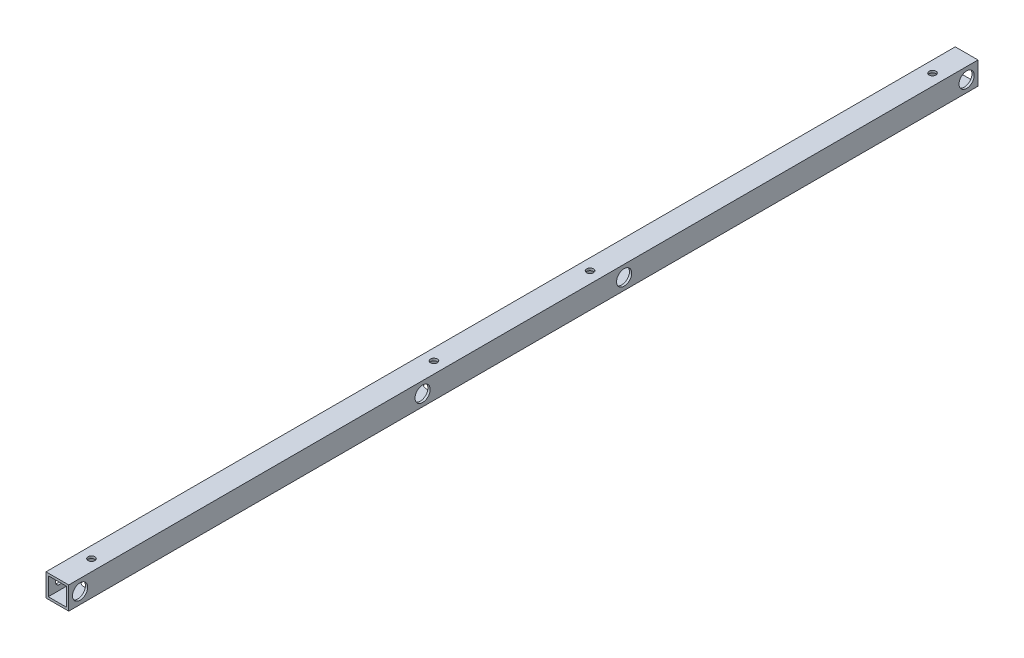
SolidWorks part; units mm, degrees
material "6063-T5"
ref_plane "正面" through (0, 0, 0) normal (0, 0, 1) x (1, 0, 0)
ref_plane "平面" through (0, 0, 0) normal (0, 1, 0) x (1, 0, 0)
ref_plane "右側面" through (0, 0, 0) normal (1, 0, 0) x (0, 0, -1)
sketch "ｽｹｯﾁ1" plane through (0, 0, 0) normal (0, 0, 1) x (1, 0, 0)
  line L1 (-7.5, -7.5) -> (7.5, -7.5)
  line L2 (-7.5, -7.5) -> (-7.5, 7.5)
  line L3 (-7.5, 7.5) -> (7.5, 7.5)
  line L4 (7.5, -7.5) -> (7.5, 7.5)
  line L5 (-7.5, -7.5) -> (7.5, 7.5) construction
  line L6 (-7.5, 7.5) -> (7.5, -7.5) construction
  line L7 (-6, -6) -> (6, -6)
  line L8 (-6, -6) -> (-6, 6)
  line L9 (-6, 6) -> (6, 6)
  line L10 (6, -6) -> (6, 6)
  line L11 (-6, -6) -> (6, 6) construction
  line L12 (-6, 6) -> (6, -6) construction
  point P0 (0, 0)
  point P6 (0, 0)
  dimension "D1" = 1.5
  dimension "D2" = 15
  dimension "D3" = 15
extrude "ﾎﾞｽ - 押し出し1" add sketch "ｽｹｯﾁ1" along normal blind 600
sketch "ｽｹｯﾁ2" plane through (7.5, 0, 0) normal (1, 0, 0) x (0, 0, -1)
  line L0 (-600, -7.5) -> (0, -7.5) construction
  line L1 (0, -7.5) -> (0, 7.5) construction
  line L2 (-600, -7.5) -> (-600, 7.5) construction
  circle A4 centre (-592.5, 0) radius 2.7
  circle A8 centre (-7.5, 0) radius 2.7
  dimension "D1" = 5.4
  dimension "D2" = 7.5
  dimension "D3" = 7.5
  dimension "D4" = 7.5
  dimension "D9" = 2
extrude "ｶｯﾄ - 押し出し1" cut sketch "ｽｹｯﾁ2" against normal blind 25
sketch "ｽｹｯﾁ3" plane through (0, 7.5, 0) normal (0, 1, 0) x (1, 0, 0)
  line L1 (-7.5, -600) -> (-7.5, 0) construction
  line L2 (7.5, -600) -> (7.5, 0) construction
  line L3 (7.5, 0) -> (-7.5, 0) construction
  circle A1 centre (0, -22.5) radius 2.25
  circle A6 centre (0, -577.5) radius 2.25
  circle A7 centre (0, -248.5) radius 2.25
  circle A8 centre (0, -351.5) radius 2.25
  point P13 (-7.5, -300)
  dimension "D3" = 4.5
  dimension "D5" = 4.5
  dimension "D9" = 7.5
  dimension "D11" = 22.5
  dimension "D2" = 22.5
  dimension "D4" = 7.5
  dimension "D6" = 103
  dimension "D7" = 51.5
extrude "ｶｯﾄ - 押し出し2" cut sketch "ｽｹｯﾁ3" against normal blind 25
sketch "ｽｹｯﾁ4" plane through (7.5, 0, 0) normal (1, 0, 0) x (0, 0, -1)
  line L0 (-600, -7.5) -> (0, -7.5) construction
  line L1 (-600, 7.5) -> (0, 7.5) construction
  circle A0 centre (-366.5, 0) radius 2.7
  circle A1 centre (-233.5, 0) radius 2.7
  point P8 (-300, 7.5)
  dimension "D1" = 7.5
  dimension "D3" = 5.4
  dimension "D4" = 5.4
  dimension "D6" = 133
  dimension "D2" = 7.5
  dimension "D5" = 66.5
extrude "ｶｯﾄ - 押し出し3" cut sketch "ｽｹｯﾁ4" against normal blind 20
sketch "ｽｹｯﾁ5" plane through (7.5, 0, 0) normal (1, 0, 0) x (0, 0, -1)
  circle A0 centre (-592.5, 0) radius 5
  circle A1 centre (-366.5, 0) radius 5
  circle A2 centre (-233.5, 0) radius 5
  circle A3 centre (-7.5, 0) radius 5
  dimension "D1" = 10
  dimension "D2" = 10
  dimension "D3" = 10
  dimension "D4" = 10
extrude "ｶｯﾄ - 押し出し4" cut sketch "ｽｹｯﾁ5" against normal blind 10
sketch "ｽｹｯﾁ6" plane through (0, -7.5, 0) normal (0, -1, 0) x (-1, 0, 0)
  circle A0 centre (0, -577.5) radius 5
  circle A1 centre (0, -22.5) radius 5
  circle A2 centre (0, -248.5) radius 5
  circle A3 centre (0, -351.5) radius 5
  dimension "D1" = 10
  dimension "D2" = 10
extrude "ｶｯﾄ - 押し出し5" cut sketch "ｽｹｯﾁ6" against normal blind 10
equation "\"D7@ｽｹｯﾁ3\"= \"D6@ｽｹｯﾁ3\" / 2"
